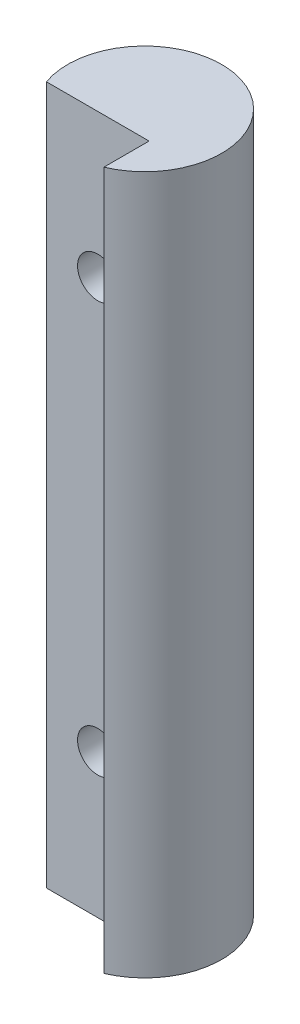
SolidWorks part; units mm, degrees
ref_plane "Top Plane" through (0, 0, 0) normal (0, 0, 1) x (1, 0, 0)
ref_plane "Front Plane" through (0, 0, 0) normal (0, 1, 0) x (1, 0, 0)
ref_plane "Right Plane" through (0, 0, 0) normal (1, 0, 0) x (0, 0, -1)
sketch "Profile Sketch" plane through (0, 0, 0) normal (0, 1, 0) x (1, 0, 0)
  circle A0 centre (0, 0) radius 4.7625
  dimension "D1" = 9.525
extrude "Boss-Extrude1" add sketch "Profile Sketch" along normal blind 43.18
sketch "Plate Relief Sketch" plane through (0, 0, 0) normal (0, -1, 0) x (1, 0, 0)
  line L1 (1.8599, 1.5875) -> (-4.4901, 1.5875)
  line L2 (1.8599, 1.5875) -> (1.8599, 4.7625)
  line L3 (1.8599, 4.7625) -> (-4.4901, 4.7625)
  line L4 (-4.4901, 1.5875) -> (-4.4901, 4.7625)
  circle A1 centre (0, 0) radius 4.7625 construction
  dimension "D1" = 3.175
  dimension "D2" = 6.35
extrude "Plate Relief Cut" cut sketch "Plate Relief Sketch" against normal up to next
sketch "Screw Mounting Sketch" plane through (0, 0, 1.5875) normal (0, 0, 1) x (1, 0, 0)
  line L0 (-1.3151, 43.18) -> (-1.3151, 0) construction
  line L1 (-4.4901, 0) -> (1.8599, 0) construction
  line L2 (-4.4901, 43.18) -> (1.8599, 43.18) construction
  line L3 (-4.7625, 21.59) -> (1.8599, 21.59) construction
  line L5 (1.8599, 43.18) -> (1.8599, 0) construction
  line L6 (-4.7625, 0) -> (4.7625, 0) construction
  line L7 (-4.7625, 0) -> (4.7625, 0) construction
  point P6 (-1.3151, 34.29)
  point P7 (-1.3151, 8.89)
  dimension "D1" = 12.7
  dimension "D2" = 3.175
hole_wizard "M3x0.5 Tapped Hole1" positions "3DSketch1" profile "Sketch4" tap size "M3x0.5" standard "ANSI Metric" end condition through all
sketch3d "3DSketch1"
  point P0 (-1.3151, 34.29, 1.5875)
  point P3 (-1.3151, 8.89, 1.5875)
sketch "Sketch4" plane through (-1.3151, 34.29, 1.5875) normal (1, 0, 0) x (0, -1, 0)
  line L0 (0, 0) -> (0, 6.35)
  line L1 (0, 6.35) -> (1.25, 6.35)
  line L2 (1.25, 6.35) -> (1.25, 0)
  line L5 (1.25, 0) -> (0, 0)
  line L11 (0, -6.35) -> (0, 107.95) construction
  dimension "Thru Tap Drill Dia." = 2.5
  dimension "Thru Tap Drill Depth" = 6.35
cosmetic thread "Hole Thread1" parameters "D2"=3
cosmetic thread "Hole Thread2" parameters "D2"=3
